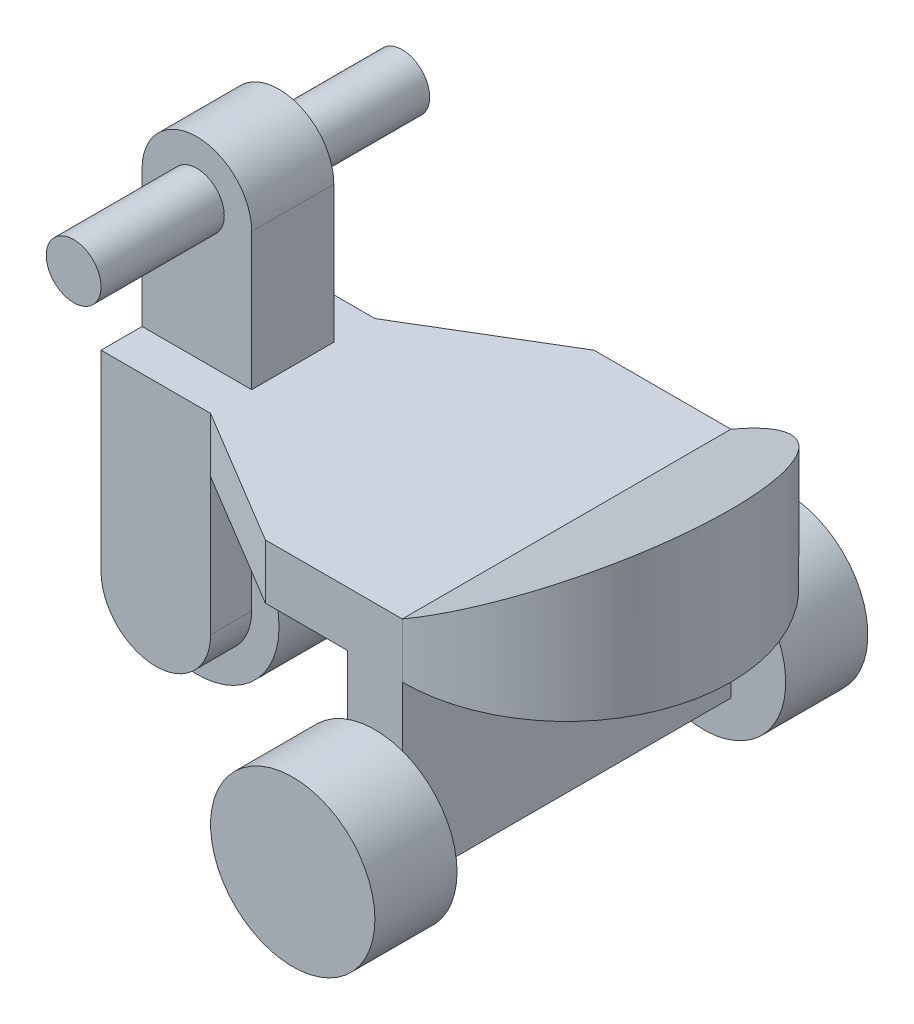
SolidWorks part; units mm, degrees
ref_plane "Front" through (0, 0, 0) normal (0, 0, 1) x (1, 0, 0)
ref_plane "Top" through (0, 0, 0) normal (0, 1, 0) x (1, 0, 0)
ref_plane "Right" through (0, 0, 0) normal (1, 0, 0) x (0, 0, -1)
sketch "Sketch1" plane through (0, 0, 0) normal (0, 1, 0) x (1, 0, 0)
  line L1 (0, -60) -> (-50, -60)
  line L2 (0, 60) -> (-50, 60)
  line L9 (-100, 15) -> (-100, -15)
  line L10 (-140, 30) -> (-140, 15)
  line L11 (-50, 60) -> (-100, 30)
  line L12 (-100, -30) -> (-50, -60)
  line L13 (-100, 60) -> (-100, -60) construction
  line L14 (-140, 60) -> (-140, -60) construction
  line L20 (-140, -15) -> (-140, -30)
  line L21 (-100, 30) -> (-140, 30)
  line L23 (-100, -30) -> (-140, -30)
  line L24 (-100, -15) -> (-140, -15)
  line L25 (-100, 15) -> (-140, 15)
  arc A1 (0, -60) -> (0, 60) centre (0, 0) ccw
extrude "Extrude1" add sketch "Sketch1" along normal blind 20
sketch "Sketch2" plane through (0, 20, 0) normal (0, 1, 0) x (-1, 0, 0)
  line L0 (0, -60) -> (0, 60)
  arc A0 (0, 60) -> (0, -60) centre (0, 0) ccw
extrude "Extrude2" add sketch "Sketch2" along normal blind 40 contours A0 L0
sketch "Sketch4" plane through (0, 0, 0) normal (0, 0, 1) x (1, 0, 0)
  line L0 (0, 20) -> (76.1025, 63.9378)
  line L3 (55, 100.4883) -> (76.1025, 63.9378)
  line L5 (-21.1025, 56.5505) -> (0, 20)
  line L6 (55, 100.4883) -> (-21.1025, 56.5505)
extrude "Cut-Extrude1" cut sketch "Sketch4" against normal mid plane 120
sketch "Sketch5" plane through (0, 0, 0) normal (0, -1, 0) x (1, 0, 0)
  line L0 (0, 60) -> (0, -60)
  line L1 (-20, 60) -> (-20, -60)
  line L2 (0, 60) -> (-20, 60)
  line L3 (0, -60) -> (-20, -60)
  line L4 (-100, 15) -> (-140, 15)
  line L5 (-140, 15) -> (-140, 30)
  line L6 (-140, 30) -> (-100, 30)
  line L7 (-100, 30) -> (-100, 15)
  line L8 (-100, -15) -> (-140, -15)
  line L9 (-140, -15) -> (-140, -30)
  line L10 (-140, -30) -> (-100, -30)
  line L11 (-100, -30) -> (-100, -15)
  line L12 (-100, -15) -> (-100.7146, -15.6369)
extrude "Extrude3" add sketch "Sketch5" along normal blind 50
sketch "Sketch6" plane through (0, -50, 0) normal (0, -1, 0) x (1, 0, 0)
  line L1 (-20, 60) -> (0, 60)
  line L2 (-20, 60) -> (-20, -60)
  line L3 (-20, -60) -> (0, -60)
  line L4 (0, 60) -> (0, -60)
extrude "Extrude4" add sketch "Sketch6" along normal blind 15
sketch "Sketch7" plane through (0, 0, 30) normal (0, 0, 1) x (1, 0, 0)
  line L0 (-100, -50) -> (-140, -50) construction
  circle A0 centre (-120, -50) radius 20
extrude "Extrude5" add sketch "Sketch7" against normal blind 15
sketch "Sketch8" plane through (0, 0, -15) normal (0, 0, 1) x (1, 0, 0)
  line L0 (-100, -50) -> (-140, -50) construction
  circle A0 centre (-120, -50) radius 20
extrude "Extrude6" add sketch "Sketch8" against normal blind 15
sketch "Sketch9" plane through (0, 0, 60) normal (0, 0, 1) x (1, 0, 0)
  circle A0 centre (-10, -50) radius 30
extrude "Extrude7" add sketch "Sketch9" along normal blind 30 separate body
sketch "Sketch10" plane through (0, 0, -60) normal (0, 0, -1) x (-1, 0, 0)
  circle A0 centre (10, -50) radius 30
extrude "Extrude8" add sketch "Sketch10" along normal blind 30 separate body
sketch "Sketch12" plane through (0, 0, -15) normal (0, 0, 1) x (1, 0, 0)
  circle A0 centre (-120, -50) radius 30
extrude "Extrude9" add sketch "Sketch12" along normal blind 30 separate body
sketch "Sketch13" plane through (0, 20, 0) normal (0, 1, 0) x (-1, 0, 0)
  line L1 (100, -15) -> (140, -15)
  line L2 (100, -15) -> (100, 15)
  line L3 (100, 15) -> (140, 15)
  line L4 (140, -15) -> (140, 15)
extrude "Extrude10" add sketch "Sketch13" along normal blind 50 and the other way blind 20 separate body
sketch "Sketch14" plane through (0, 0, 15) normal (0, 0, 1) x (1, 0, 0)
  line L0 (-140, 70) -> (-100, 70) construction
  circle A0 centre (-120, 70) radius 20
extrude "Extrude12" add sketch "Sketch14" against normal blind 30 separate body
combine bodies "Combine1" operation type add bodies to combine 116 118
sketch "Sketch15" plane through (0, 0, 15) normal (0, 0, 1) x (1, 0, 0)
  circle A0 centre (-120, 70) radius 10
extrude "Extrude13" add sketch "Sketch15" along normal blind 45 separate body
sketch "Sketch16" plane through (0, 0, -15) normal (0, 0, -1) x (-1, 0, 0)
  circle A0 centre (120, 70) radius 10
extrude "Extrude14" add sketch "Sketch16" along normal blind 45 separate body
